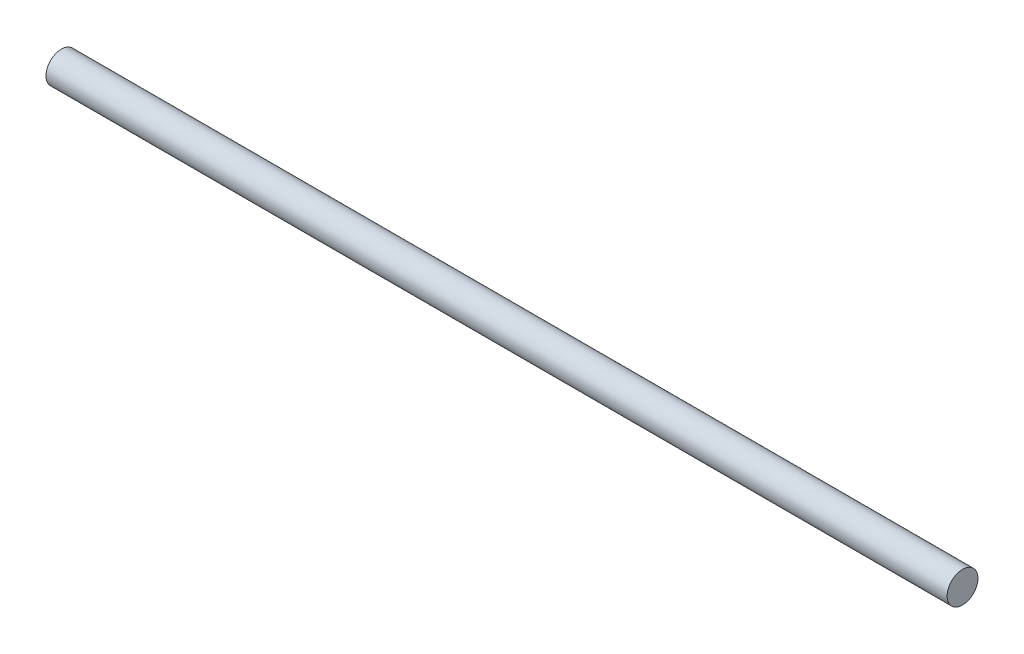
SolidWorks part; units mm, degrees
ref_plane "Front Plane" through (0, 0, 0) normal (0, 0, 1) x (1, 0, 0)
ref_plane "Top Plane" through (0, 0, 0) normal (0, 1, 0) x (1, 0, 0)
ref_plane "Right Plane" through (0, 0, 0) normal (1, 0, 0) x (0, 0, -1)
sketch "Sketch1" plane through (0, 0, 0) normal (1, 0, 0) x (0, 0, -1)
  circle A0 centre (0, 0) radius 15
extrude "Boss-Extrude1" add sketch "Sketch1" along normal blind 875
